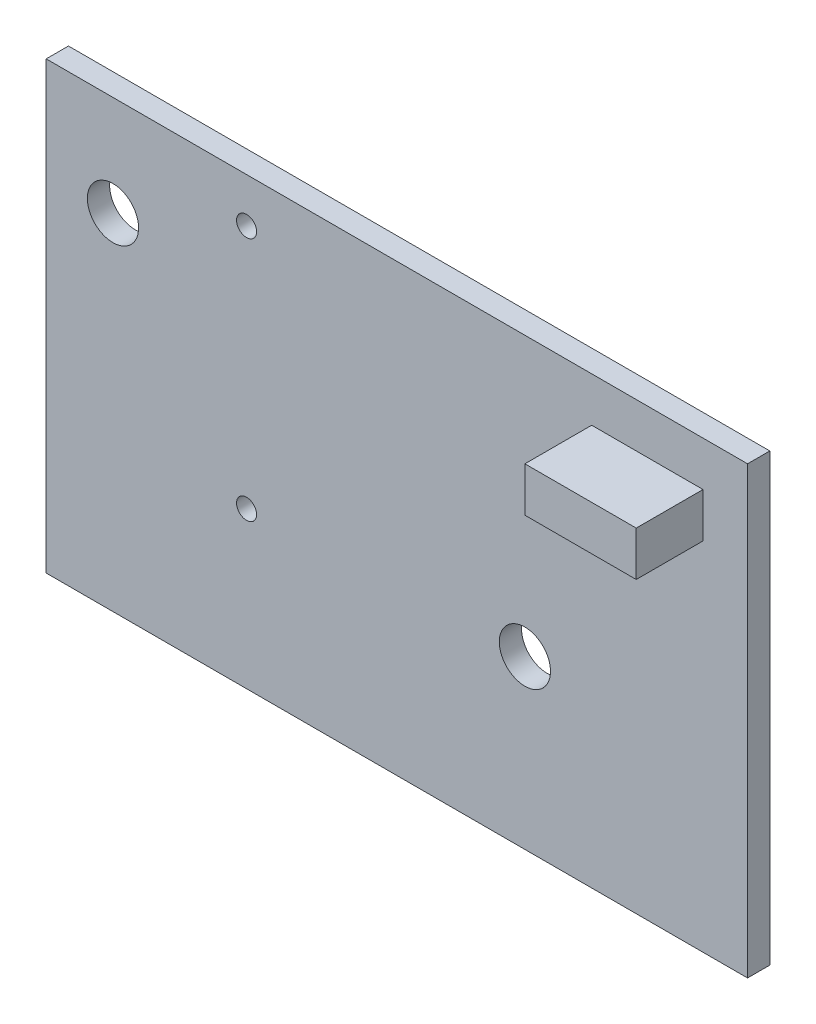
SolidWorks part; units mm, degrees
ref_plane "Спереди" through (0, 0, 0) normal (0, 0, 1) x (1, 0, 0)
ref_plane "Сверху" through (0, 0, 0) normal (0, 1, 0) x (1, 0, 0)
ref_plane "Справа" through (0, 0, 0) normal (1, 0, 0) x (0, 0, -1)
sketch "Эскиз1" plane through (0, 0, 0) normal (0, 0, 1) x (1, 0, 0)
  line L1 (0, 0) -> (31.5, 0)
  line L2 (0, 0) -> (0, 20)
  line L3 (0, 20) -> (31.5, 20)
  line L4 (31.5, 0) -> (31.5, 20)
  circle A0 centre (3, 15.5) radius 1.15
  circle A1 centre (21.5, 7.5) radius 1.15
  circle A2 centre (9, 18) radius 0.45
  circle A3 centre (9, 7) radius 0.45
  dimension "D3" = 4.5
  dimension "D5" = 8
  dimension "D6" = 18.5
  dimension "D7" = 2.3
  dimension "D11" = 0.9
  dimension "D1" = 31.5
  dimension "D2" = 20
  dimension "D4" = 3
  dimension "D8" = 9
  dimension "D9" = 11
  dimension "D10" = 2
extrude "Бобышка-Вытянуть1" add sketch "Эскиз1" along normal blind 1
sketch "Эскиз2" plane through (0, 0, 1) normal (0, 0, 1) x (1, 0, 0)
  line L0 (31.5, 20) -> (0, 20) construction
  line L1 (24.5, 18) -> (29.5, 18)
  line L2 (24.5, 18) -> (24.5, 16)
  line L3 (24.5, 16) -> (29.5, 16)
  line L4 (29.5, 18) -> (29.5, 16)
  line L5 (31.5, 0) -> (31.5, 20) construction
  dimension "D1" = 2
  dimension "D2" = 2
  dimension "D3" = 5
  dimension "D4" = 2
extrude "Бобышка-Вытянуть2" add sketch "Эскиз2" along normal blind 3
